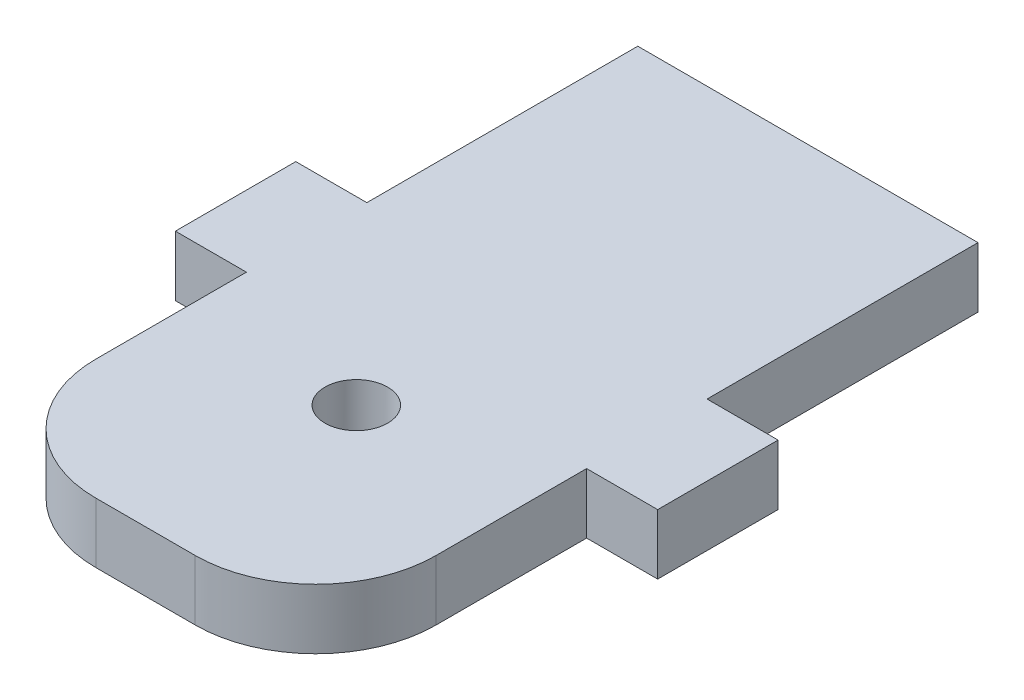
SolidWorks part; units mm, degrees
ref_plane "Front Plane" through (0, 0, 0) normal (0, 0, 1) x (1, 0, 0)
ref_plane "Top Plane" through (0, 0, 0) normal (0, 1, 0) x (1, 0, 0)
ref_plane "Right Plane" through (0, 0, 0) normal (1, 0, 0) x (0, 0, -1)
sketch "Sketch1" plane through (0, 0, 0) normal (0, 1, 0) x (1, 0, 0)
  line L1 (-14.125, -27.5) -> (14.125, -27.5)
  line L2 (-14.125, -27.5) -> (-14.125, 27.5)
  line L3 (-14.125, 27.5) -> (14.125, 27.5)
  line L4 (14.125, -27.5) -> (14.125, 27.5)
  line L5 (-14.125, -27.5) -> (14.125, 27.5) construction
  line L6 (-14.125, 27.5) -> (14.125, -27.5) construction
  point P0 (0, 0)
  dimension "D1" = 28.25
  dimension "D2" = 55
extrude "Boss-Extrude1" add sketch "Sketch1" along normal blind 5
sketch "Sketch2" plane through (0, 5, 0) normal (0, 1, 0) x (1, 0, 0)
  line L0 (-14.125, -27.5) -> (14.125, -27.5) construction
  line L1 (-10, 20.5) -> (10, 20.5) construction
  line L2 (-10, 20.5) -> (-10, -20) construction
  line L3 (-10, -20) -> (10, -20) construction
  line L4 (10, 20.5) -> (10, -20) construction
  line L5 (-10, 20.5) -> (10, -20) construction
  line L6 (-10, -20) -> (10, 20.5) construction
  circle A0 centre (0, -10) radius 2.6
  point P0 (0, 0.25)
  dimension "D4" = 5.2
  dimension "D5" = 10
  dimension "D1" = 40.5
  dimension "D2" = 20
  dimension "D3" = 7.5
sketch "Sketch3" plane through (0, 5, 0) normal (0, 1, 0) x (1, 0, 0)
  line L0 (-14.125, 5) -> (-20.025, 5)
  line L1 (-14.125, 5) -> (-14.125, -5)
  line L2 (-14.125, -5) -> (-20.025, -5)
  line L3 (-20.025, 5) -> (-20.025, -5)
  line L4 (0, 30.9283) -> (0, 24.4049) construction
  line L5 (14.125, -5) -> (20.025, -5)
  line L6 (20.025, 5) -> (20.025, -5)
  line L7 (14.125, 5) -> (20.025, 5)
  line L8 (14.125, 5) -> (14.125, -5)
  line L9 (-14.125, 27.5) -> (-14.125, -27.5) construction
  point P10 (-20.025, 0)
  dimension "D2" = 10
  dimension "D3" = 5.9
extrude "Boss-Extrude2" add sketch "Sketch3" against normal up to surface (5 mm away) up to face at (0, 0, 0)
extrude "Cut-Extrude1" cut sketch "Sketch2" against normal blind 10
fillet "Fillet1" radius 10 2 edges at (14.125, 2.5, 27.5) (-14.125, 2.5, 27.5)
equation "\"e\" = 5.9"
equation "\"D3@Sketch3\"= \"e\""
